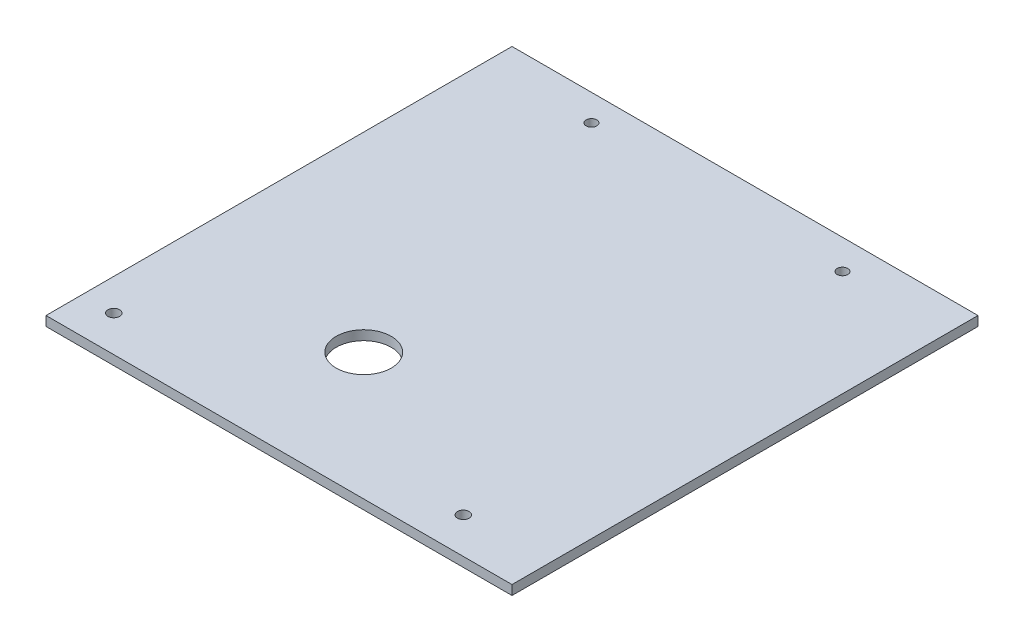
SolidWorks part; units mm, degrees
ref_plane "Front" through (0, 0, 0) normal (0, 0, 1) x (1, 0, 0)
ref_plane "Top" through (0, 0, 0) normal (0, 1, 0) x (1, 0, 0)
ref_plane "Right" through (0, 0, 0) normal (1, 0, 0) x (0, 0, -1)
sketch "Sketch1" plane through (0, 0, 0) normal (0, 1, 0) x (1, 0, 0)
  line L1 (-110, -110) -> (110, -110)
  line L2 (-110, -110) -> (-110, 110)
  line L3 (-110, 110) -> (110, 110)
  line L4 (110, -110) -> (110, 110)
  line L5 (-110, -110) -> (110, 110) construction
  line L6 (-110, 110) -> (110, -110) construction
  point P0 (0, 0)
  dimension "D1" = 220
  dimension "D2" = 220
extrude "Boss-Extrude1" add sketch "Sketch1" along normal blind 4.5
sketch "Sketch2" plane through (0, 4.5, 0) normal (0, 1, 0) x (1, 0, 0)
  line L5 (-110, -110) -> (110, -110) construction
  line L6 (-110, 110) -> (-110, -110) construction
  circle A0 centre (-20, -50) radius 13
  dimension "D4" = 26
  dimension "D5" = 90
  dimension "D9" = 60
extrude "Cut-Extrude1" cut sketch "Sketch2" against normal up to next
sketch "Sketch3" plane through (0, 4.5, 0) normal (0, 1, 0) x (1, 0, 0)
  line L0 (-110, 110) -> (-110, -110) construction
  line L1 (-110, -110) -> (110, -110) construction
  circle A0 centre (-95, -93) radius 2.75
  circle A1 centre (70, -93) radius 2.75
  dimension "D4" = 5.5
  dimension "D5" = 5.5
  dimension "D1" = 15
  dimension "D2" = 17
  dimension "D3" = 165
  dimension "D6" = 17
extrude "Cut-Extrude2" cut sketch "Sketch3" against normal up to next
sketch "Sketch4" plane through (0, 0, 0) normal (0, -1, 0) x (-1, 0, 0)
  circle A0 centre (-60, 96) radius 2.5
  circle A1 centre (60, 97.5) radius 2.5
extrude "Cut-Extrude3" cut sketch "Sketch4" against normal up to next
